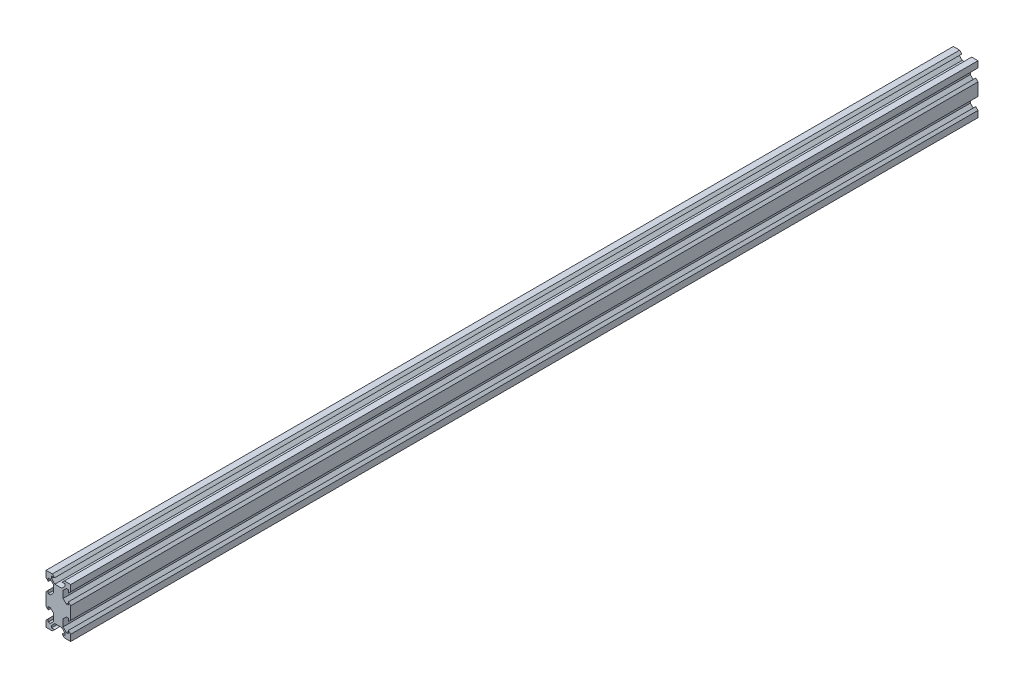
SolidWorks part; units mm, degrees
ref_plane "Front Plane" through (0, 0, 0) normal (0, 0, 1) x (1, 0, 0)
ref_plane "Top Plane" through (0, 0, 0) normal (0, 1, 0) x (1, 0, 0)
ref_plane "Right Plane" through (0, 0, 0) normal (1, 0, 0) x (0, 0, -1)
sketch "Sketch1" plane through (0, 0, 0) normal (0, 0, 1) x (1, 0, 0)
  line L1 (0, 0) -> (20, 0)
  line L2 (0, 0) -> (0, 40)
  line L3 (0, 40) -> (20, 40)
  line L4 (20, 0) -> (20, 40)
  line L5 (0, 0) -> (20, 40) construction
  line L6 (0, 40) -> (20, 0) construction
  point P4 (10, 20)
  dimension "D1" = 20
  dimension "D2" = 40
extrude "Boss-Extrude1" add sketch "Sketch1" along normal blind 735.0125
sketch "Sketch2" plane through (0, 0, 735.0125) normal (0, 0, 1) x (1, 0, 0)
  line L0 (5.12, 40) -> (6.94, 38.18)
  line L1 (20, 40) -> (0, 40) construction
  line L3 (13.06, 38.18) -> (14.88, 40)
  line L4 (0, 40) -> (20, 40) construction
  line L5 (20, 40) -> (10, 40) construction
  line L6 (10, 40) -> (10, 38.18) construction
  line L7 (5.12, 40) -> (14.88, 40)
  line L8 (6.94, 38.18) -> (4.5, 38.18)
  line L9 (4.5, 38.18) -> (4.5, 36.4758)
  line L10 (4.5, 36.4758) -> (7.1658, 33.81)
  line L11 (7.1658, 33.81) -> (12.8342, 33.81)
  line L12 (12.8342, 33.81) -> (15.5, 36.4758)
  line L13 (15.5, 36.4758) -> (15.5, 38.18)
  line L14 (15.5, 38.18) -> (13.06, 38.18)
  line L15 (20, 40) -> (0, 20) construction
  line L16 (0, 40) -> (0, 0) construction
  line L17 (20, 30) -> (18.18, 30) construction
  line L18 (18.18, 35.5) -> (18.18, 33.06)
  line L19 (16.4758, 35.5) -> (18.18, 35.5)
  line L20 (13.81, 32.8342) -> (16.4758, 35.5)
  line L21 (13.81, 27.1658) -> (13.81, 32.8342)
  line L22 (16.4758, 24.5) -> (13.81, 27.1658)
  line L23 (18.18, 24.5) -> (16.4758, 24.5)
  line L24 (18.18, 26.94) -> (18.18, 24.5)
  line L25 (20, 25.12) -> (20, 34.88)
  line L26 (18.18, 33.06) -> (20, 34.88)
  line L28 (20, 25.12) -> (18.18, 26.94)
  line L29 (0, 20) -> (20, 20) construction
  line L30 (20, 0) -> (20, 40) construction
  line L31 (20, 10) -> (18.18, 10) construction
  line L32 (10, 0) -> (10, 1.82) construction
  line L33 (20, 0) -> (10, 0) construction
  line L34 (20, 14.88) -> (18.18, 13.06)
  line L36 (18.18, 6.94) -> (20, 5.12)
  line L37 (20, 14.88) -> (20, 5.12)
  line L38 (18.18, 13.06) -> (18.18, 15.5)
  line L39 (18.18, 15.5) -> (16.4758, 15.5)
  line L40 (16.4758, 15.5) -> (13.81, 12.8342)
  line L41 (13.81, 12.8342) -> (13.81, 7.1658)
  line L42 (13.81, 7.1658) -> (16.4758, 4.5)
  line L43 (16.4758, 4.5) -> (18.18, 4.5)
  line L44 (18.18, 4.5) -> (18.18, 6.94)
  line L45 (15.5, 1.82) -> (13.06, 1.82)
  line L46 (15.5, 3.5242) -> (15.5, 1.82)
  line L47 (12.8342, 6.19) -> (15.5, 3.5242)
  line L48 (7.1658, 6.19) -> (12.8342, 6.19)
  line L49 (4.5, 3.5242) -> (7.1658, 6.19)
  line L50 (4.5, 1.82) -> (4.5, 3.5242)
  line L51 (6.94, 1.82) -> (4.5, 1.82)
  line L52 (5.12, 0) -> (14.88, 0)
  line L53 (13.06, 1.82) -> (14.88, 0)
  line L55 (5.12, 0) -> (6.94, 1.82)
  line L56 (10, 40) -> (10, 0) construction
  line L57 (0, 10) -> (1.82, 10) construction
  line L58 (0, 30) -> (1.82, 30) construction
  line L59 (1.82, 4.5) -> (1.82, 6.94)
  line L60 (3.5242, 4.5) -> (1.82, 4.5)
  line L61 (6.19, 7.1658) -> (3.5242, 4.5)
  line L62 (6.19, 12.8342) -> (6.19, 7.1658)
  line L63 (3.5242, 15.5) -> (6.19, 12.8342)
  line L64 (1.82, 15.5) -> (3.5242, 15.5)
  line L65 (1.82, 13.06) -> (1.82, 15.5)
  line L66 (0, 14.88) -> (0, 5.12)
  line L67 (1.82, 6.94) -> (0, 5.12)
  line L69 (0, 14.88) -> (1.82, 13.06)
  line L70 (0, 25.12) -> (1.82, 26.94)
  line L72 (1.82, 33.06) -> (0, 34.88)
  line L73 (0, 25.12) -> (0, 34.88)
  line L74 (1.82, 26.94) -> (1.82, 24.5)
  line L75 (1.82, 24.5) -> (3.5242, 24.5)
  line L76 (3.5242, 24.5) -> (6.19, 27.1658)
  line L77 (6.19, 27.1658) -> (6.19, 32.8342)
  line L78 (6.19, 32.8342) -> (3.5242, 35.5)
  line L79 (3.5242, 35.5) -> (1.82, 35.5)
  line L80 (1.82, 35.5) -> (1.82, 33.06)
  dimension "D1" = 90
  dimension "D3" = 6.12
  dimension "D5" = 11
  dimension "D6" = 6.19
  dimension "D7" = 1.38
extrude "Cut-Extrude1" cut sketch "Sketch2" against normal through all
